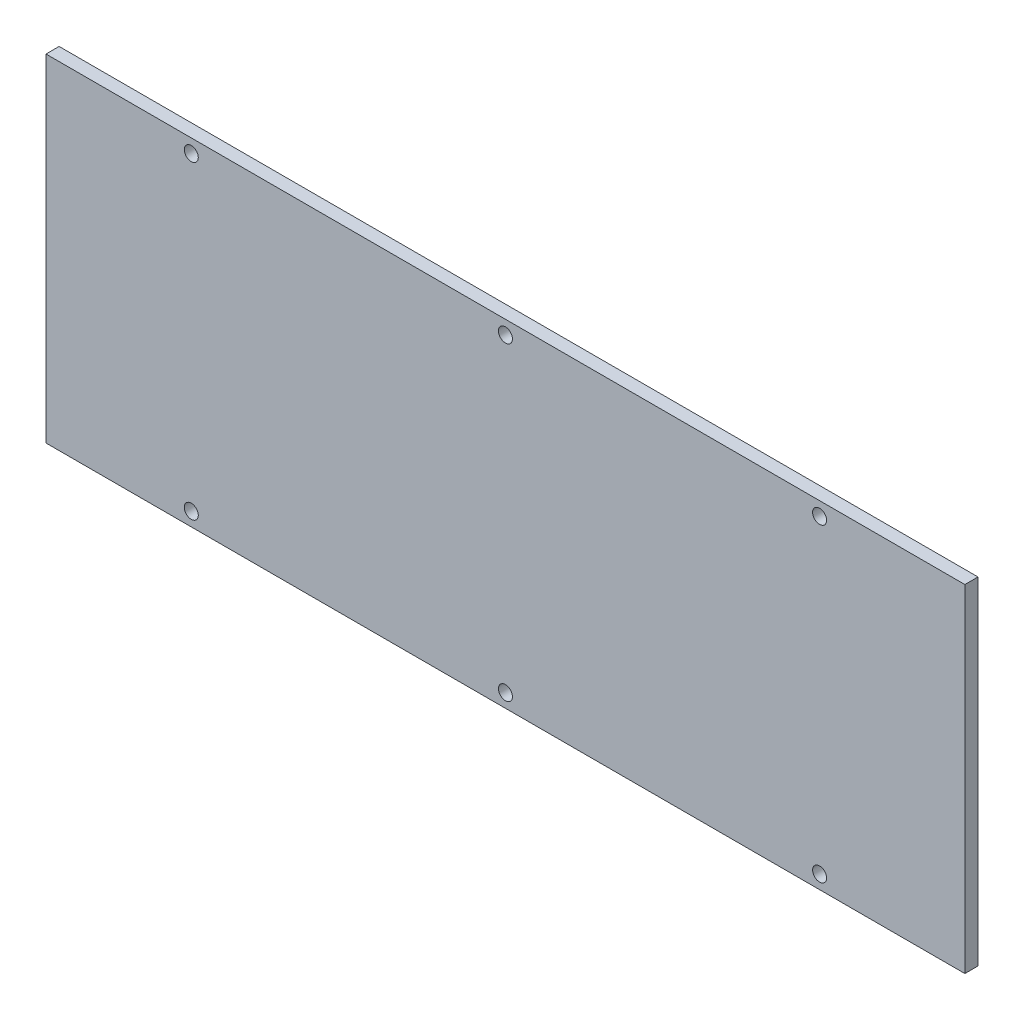
SolidWorks part; units mm, degrees
ref_plane "Alzado" through (0, 0, 0) normal (0, 0, 1) x (1, 0, 0)
ref_plane "Planta" through (0, 0, 0) normal (0, 1, 0) x (1, 0, 0)
ref_plane "Vista lateral" through (0, 0, 0) normal (1, 0, 0) x (0, 0, -1)
sketch "Croquis1" plane through (0, 0, 0) normal (0, 0, 1) x (1, 0, 0)
  line L0 (-105, 35.4) -> (-71.8, 35.4) construction
  line L1 (105, -38.5) -> (-105, -38.5)
  line L2 (105, -38.5) -> (105, 38.5)
  line L3 (105, 38.5) -> (-105, 38.5)
  line L4 (-105, -38.5) -> (-105, 38.5)
  line L5 (105, -38.5) -> (-105, 38.5) construction
  line L6 (105, 38.5) -> (-105, -38.5) construction
  line L7 (-71.8, 35.4) -> (0, 35.4) construction
  line L8 (0, 35.4) -> (71.8, 35.4) construction
  line L9 (71.8, 35.4) -> (105, 35.4) construction
  line L10 (-105, 0) -> (105, 0) construction
  circle A0 centre (0, 35.4) radius 1.6
  circle A1 centre (-71.8, 35.4) radius 1.6
  circle A2 centre (71.8, 35.4) radius 1.6
  circle A3 centre (71.8, -35.4) radius 1.6
  circle A4 centre (0, -35.4) radius 1.6
  circle A5 centre (-71.8, -35.4) radius 1.6
  point P0 (0, 0)
  dimension "D5" = 3.2
  dimension "D1" = 210
  dimension "D2" = 77
  dimension "D3" = 3.1
  dimension "D4" = 71.8
extrude "Saliente-Extruir1" add sketch "Croquis1" along normal blind 3
